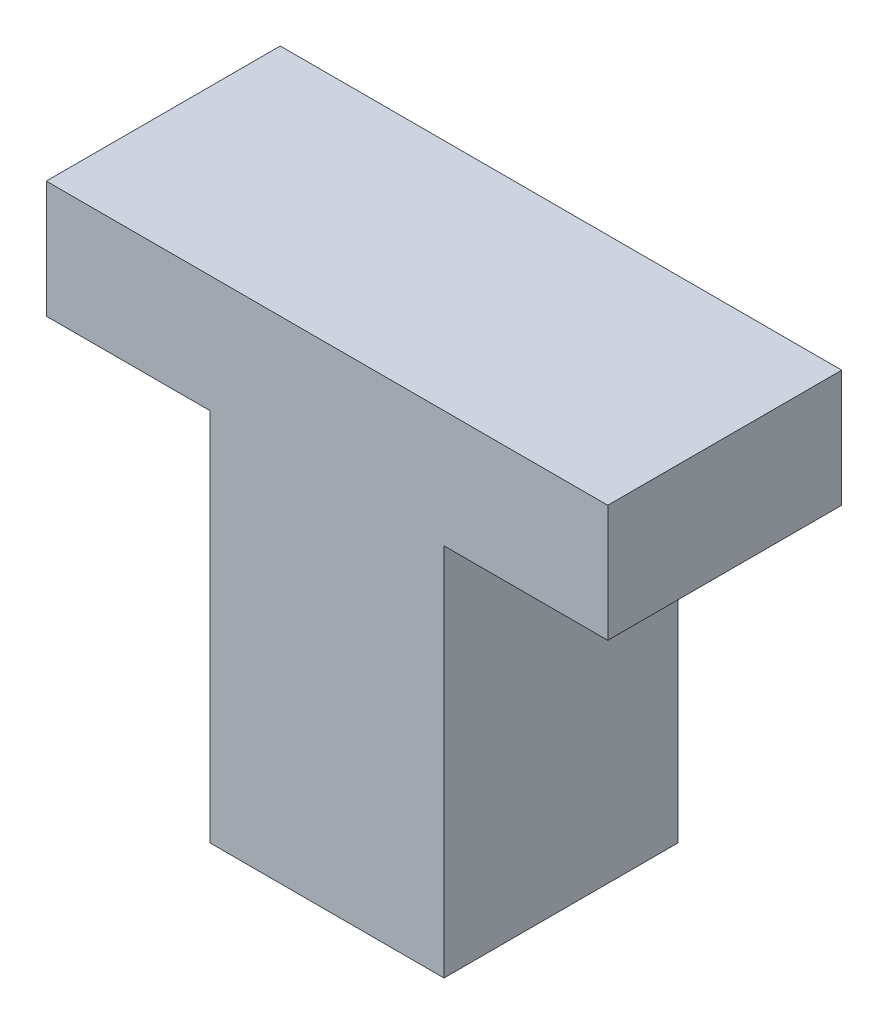
SolidWorks part; units mm, degrees
ref_plane "Front Plane" through (0, 0, 0) normal (0, 0, 1) x (1, 0, 0)
ref_plane "Top Plane" through (0, 0, 0) normal (0, 1, 0) x (1, 0, 0)
ref_plane "Right Plane" through (0, 0, 0) normal (1, 0, 0) x (0, 0, -1)
sketch "Sketch1" plane through (0, 0, 0) normal (0, 0, 1) x (1, 0, 0)
  line L0 (0, 0) -> (0, 8)
  line L1 (0, 8) -> (-3.5, 8)
  line L2 (-3.5, 8) -> (-3.5, 10.5)
  line L3 (-3.5, 10.5) -> (8.5, 10.5)
  line L4 (8.5, 10.5) -> (8.5, 8)
  line L5 (8.5, 8) -> (5, 8)
  line L6 (5, 8) -> (5, 0)
  line L7 (5, 0) -> (0, 0)
  dimension "D1" = 12
  dimension "D2" = 3.5
  dimension "D3" = 5
  dimension "D4" = 2.5
  dimension "D5" = 10.5
extrude "Boss-Extrude1" add sketch "Sketch1" along normal blind 5
